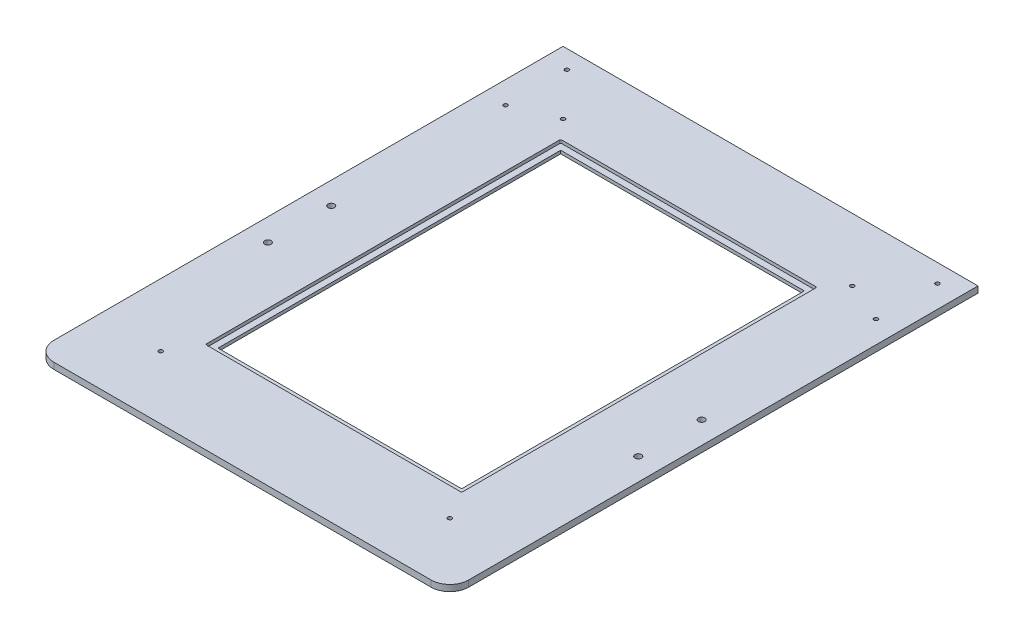
SolidWorks part; units mm, degrees
material "6061 Alloy"
ref_plane "Front Plane" through (0, 0, 0) normal (0, 0, 1) x (1, 0, 0)
ref_plane "Top Plane" through (0, 0, 0) normal (0, 1, 0) x (1, 0, 0)
ref_plane "Right Plane" through (0, 0, 0) normal (1, 0, 0) x (0, 0, -1)
sketch "Sketch1" plane through (0, 0, 0) normal (0, 1, 0) x (1, 0, 0)
  line L0 (209.55, 533.4) -> (209.55, 444.5) construction
  line L1 (0, 0) -> (419.1, 0)
  line L2 (0, 0) -> (0, 533.4)
  line L3 (0, 533.4) -> (419.1, 533.4)
  line L4 (419.1, 0) -> (419.1, 533.4)
  line L5 (86.5187, 444.5) -> (332.5812, 444.5)
  line L6 (86.5187, 444.5) -> (86.5187, 98.425)
  line L7 (86.5187, 98.425) -> (332.5813, 98.425)
  line L8 (332.5812, 444.5) -> (332.5813, 98.425)
  dimension "D1" = 246.0625
  dimension "D2" = 346.075
  dimension "D3" = 88.9
  dimension "D4" = 533.4
  dimension "D5" = 419.1
extrude "Overall shape" add sketch "Sketch1" along normal blind 6.35
sketch "Sketch5" plane through (0, 6.35, 0) normal (0, 1, 0) x (1, 0, 0)
  line L14 (80.1688, 92.075) -> (338.9313, 92.075)
  line L15 (338.9313, 92.075) -> (338.9312, 450.85)
  line L16 (80.1687, 450.85) -> (80.1688, 92.075)
  line L17 (338.9312, 450.85) -> (80.1687, 450.85)
  line L18 (80.1688, 92.075) -> (338.9313, 92.075)
  line L19 (338.9313, 92.075) -> (338.9312, 450.85)
  line L20 (80.1687, 450.85) -> (80.1688, 92.075)
  line L21 (338.9312, 450.85) -> (80.1687, 450.85)
  dimension "D1" = 6.35
extrude "Glass inset cut" cut sketch "Sketch5" against normal blind 3.2
fillet "Glass inset fillets" radius 1.27 4 edges at (338.9313, 4.75, -92.075) (80.1688, 4.75, -92.075) (338.9312, 4.75, -450.85) (80.1687, 4.75, -450.85)
ref_plane "Center plane" through (209.55, 0, 0) normal (1, 0, 0) x (0, 0, -1)
sketch "Sketch8" plane through (0, 6.35, 0) normal (0, 1, 0) x (1, 0, 0)
  line L0 (209.55, 533.4) -> (209.55, 0) construction
  line L1 (209.55, -3.4925) -> (209.55, 3.4925) construction
  line L2 (190.3286, 0) -> (190.3286, 533.4) construction
  line L3 (0, 0) -> (419.1, 0) construction
  line L4 (419.1, 533.4) -> (0, 533.4) construction
  line L5 (228.7715, 0) -> (228.7715, 533.4) construction
  line L6 (190.3285, 100.1522) -> (198.1517, 100.1522) construction
  line L7 (198.1517, 100.1522) -> (198.1517, 49.4665) construction
  line L8 (228.7715, 106.6546) -> (220.9483, 106.6546) construction
  line L9 (220.9483, 106.6546) -> (220.9483, 57.6072) construction
  line L10 (190.3286, 426.7454) -> (198.1518, 426.7454) construction
  line L11 (198.1518, 426.7454) -> (198.1518, 475.7928) construction
  line L12 (228.7715, 433.2478) -> (220.9483, 433.2478) construction
  line L13 (220.9483, 433.2478) -> (220.9483, 483.9335) construction
  circle A0 centre (198.1517, 100.1522) radius 1.9177
  circle A1 centre (220.9483, 106.6546) radius 1.9177
  circle A2 centre (198.1517, 49.4665) radius 1.9177
  circle A3 centre (220.9483, 57.6072) radius 1.9177
  circle A4 centre (198.1518, 426.7454) radius 1.9177 construction
  circle A5 centre (220.9483, 433.2478) radius 1.9177 construction
  circle A6 centre (198.1518, 475.7928) radius 1.9177
  circle A7 centre (220.9483, 483.9335) radius 1.9177
  point P22 (209.55, 266.7)
  point P34 (254, 342.9)
  dimension "D3" = 7.8232
  dimension "D4" = 3.8354
  dimension "D9" = 3.8354
  dimension "D1" = 19.2215
  dimension "D2" = 19.2215
  dimension "D5" = 49.4665
  dimension "D6" = 57.6072
  dimension "D7" = 100.1522
  dimension "D8" = 106.6546
  dimension "D10" = 7.8232
  dimension "D11" = 106.6546
  dimension "D12" = 100.1522
  dimension "D13" = 57.6072
  dimension "D14" = 49.4665
extrude "Y axis bracket holes" [suppressed] cut sketch "Sketch8" against normal through all
fillet "Fillet1" radius 19.05 2 edges at (419.1, 3.175, 0) (0, 3.175, 0)
sketch "Sketch12" plane through (0, 6.35, 0) normal (0, 1, 0) x (1, 0, 0)
  line L0 (419.1, 533.4) -> (0, 533.4) construction
  line L1 (0, 533.4) -> (0, 19.05) construction
  line L2 (419.1, 19.05) -> (419.1, 533.4) construction
  line L3 (19.05, 0) -> (400.05, 0) construction
  point P0 (63.5, 469.9)
  point P1 (355.6, 469.9)
  point P2 (63.5, 63.5)
  point P3 (355.6, 63.5)
  dimension "D1" = 63.5
  dimension "D2" = 63.5
  dimension "D3" = 63.5
  dimension "D4" = 63.5
hole_wizard "#10-32 Tapped Hole3" positions "Sketch14" profile "Sketch13" tap size "#10-32" standard "ANSI Inch" end condition up to next
sketch "Sketch14" plane through (0, 6.35, 0) normal (0, 1, 0) x (1, 0, 0)
  point P0 (63.5, 469.9)
  point P3 (355.6, 469.9)
  point P6 (355.6, 63.5)
  point P9 (63.5, 63.5)
cosmetic thread "Hole Thread1" parameters "D2"=4.826
cosmetic thread "Hole Thread2" parameters "D2"=4.826
cosmetic thread "Hole Thread3" parameters "D2"=4.826
cosmetic thread "Hole Thread4" parameters "D2"=4.826
sketch "Sketch13" plane through (63.5, 6.35, -469.9) normal (1, 0, 0) x (0, 0, 1)
  line L0 (0, 0) -> (0, 6.35)
  line L1 (0, 6.35) -> (2.0193, 6.35)
  line L2 (2.0193, 6.35) -> (2.0193, 0)
  line L5 (2.0193, 0) -> (0, 0)
  line L11 (0, -6.35) -> (0, 107.95) construction
  dimension "Thru Tap Drill Dia." = 4.0386
  dimension "Thru Tap Drill Depth" = 6.35
sketch "Sketch19" plane through (0, 6.35, 0) normal (0, 1, 0) x (1, 0, 0)
  line L0 (419.1, 533.4) -> (0, 533.4) construction
  line L1 (0, 177.8) -> (419.1, 177.8) construction
  line L2 (0, 533.4) -> (0, 19.05) construction
  line L3 (419.1, 19.05) -> (419.1, 533.4) construction
  point P0 (22.479, 514.8707)
  point P1 (22.479, 452.8185)
  point P2 (22.479, 276.7965)
  point P3 (22.479, 212.7504)
  point P4 (396.621, 514.8707)
  point P5 (396.621, 452.8185)
  point P6 (396.621, 276.7965)
  point P7 (396.621, 212.7504)
  dimension "D1" = 80.5815
  dimension "D2" = 18.5293
  dimension "D3" = 98.9965
  dimension "D4" = 34.9504
  dimension "D5" = 22.479
  dimension "D6" = 22.479
  dimension "D7" = 355.6
hole_wizard "#10-32 Tapped Hole7" positions "Sketch21" profile "Sketch20" tap size "#10-32" standard "ANSI Inch" end condition up to next
sketch "Sketch21" plane through (0, 6.35, 0) normal (0, 1, 0) x (1, 0, 0)
  point P0 (22.479, 514.8707)
  point P3 (22.479, 452.8185)
  point P6 (396.621, 514.8707)
  point P9 (396.621, 452.8185)
cosmetic thread "Hole Thread5" parameters "D2"=4.826
cosmetic thread "Hole Thread6" parameters "D2"=4.826
cosmetic thread "Hole Thread7" parameters "D2"=4.826
cosmetic thread "Hole Thread8" parameters "D2"=4.826
sketch "Sketch20" plane through (22.479, 6.35, -514.8707) normal (1, 0, 0) x (0, 0, 1)
  line L0 (0, 0) -> (0, 6.35)
  line L1 (0, 6.35) -> (2.0193, 6.35)
  line L2 (2.0193, 6.35) -> (2.0193, 0)
  line L5 (2.0193, 0) -> (0, 0)
  line L11 (0, -6.35) -> (0, 107.95) construction
  dimension "Thru Tap Drill Dia." = 4.0386
  dimension "Thru Tap Drill Depth" = 6.35
hole_wizard "5/16-18 Tapped Hole1" positions "Sketch23" profile "Sketch22" tap size "5/16-18" standard "ANSI Inch" end condition up to next
sketch "Sketch23" plane through (0, 6.35, 0) normal (0, 1, 0) x (1, 0, 0)
  point P0 (22.479, 276.7965)
  point P3 (22.479, 212.7504)
  point P6 (396.621, 276.7965)
  point P9 (396.621, 212.7504)
cosmetic thread "Hole Thread9" parameters "D2"=7.9375
cosmetic thread "Hole Thread10" parameters "D2"=7.9375
cosmetic thread "Hole Thread11" parameters "D2"=7.9375
cosmetic thread "Hole Thread12" parameters "D2"=7.9375
sketch "Sketch22" plane through (22.479, 6.35, -276.7965) normal (1, 0, 0) x (0, 0, 1)
  line L0 (0, 0) -> (0, 6.35)
  line L1 (0, 6.35) -> (3.2639, 6.35)
  line L2 (3.2639, 6.35) -> (3.2639, 0)
  line L5 (3.2639, 0) -> (0, 0)
  line L11 (0, -6.35) -> (0, 107.95) construction
  dimension "Thru Tap Drill Dia." = 6.5278
  dimension "Thru Tap Drill Depth" = 6.35
equation "\"glass pane length\"= 14.125"
equation "\"glass pane width\"= 10.1875"
equation "\"D1@Sketch1\"=\"glass pane width\"-\"glass lip\"*2"
equation "\"D2@Sketch1\"=\"glass pane length\"-\"glass lip\"*2"
equation "\"glass pane wall width\"= 3/4"
equation "\"glass lip\"= 1/4"
equation "\"bolt diameter\"= 0.2"
equation "\"stepper body width\"= 2.22"
equation "\"stepper mount offset\"= 0.19"
equation "\"stepper mount diameter\"= 0.19"
equation "\"thin metal\"= 0.12"
equation "\"thick metal\"= 0.25"
equation "\"D1@Overall shape\" = \"thick metal\""
equation "\"y axis stepper wall bracket thickness\"= 1"
equation "\"y axis stepper wall mount side offset\"= 1/2"
equation "\"y axis stepper wall mount top offset\"= 1/2"
equation "\"stepper shaft offset from body\"= 0.79"
equation "\"stepper spacer thickness\"= 0.2"
equation "\"y axis stepper wall height off base\"= 8"
equation "\"D4@Sketch1\" = \"base length\""
equation "\"base length\"= 21"
equation "\"D1@Sketch5\"=\"glass lip\""
equation "\"D1@Glass inset cut\" = 0.12598425"
equation "\"recognizer width\"= 2.5"
equation "\"y axis stepper wall width\"= \"stepper body width\" + 1                  "
equation "\"base width\"= 16.5"
equation "\"D5@Sketch1\" = \"base width\""
equation "\"D5@Sketch8\"=1.8275+\"thin metal\""
equation "\"D8@Sketch8\"=4.079+\"thin metal\""
equation "\"D6@Sketch8\"=2.148+\"thin metal\""
equation "\"D11@Sketch8\"=4.079+\"thin metal\""
equation "\"D12@Sketch8\"=3.823+\"thin metal\""
equation "\"D13@Sketch8\"=2.148+\"thin metal\""
equation "\"D14@Sketch8\"=1.8275+\"thin metal\""
equation "\"D7@Sketch8\" = 3.823 + \"thin metal\""
